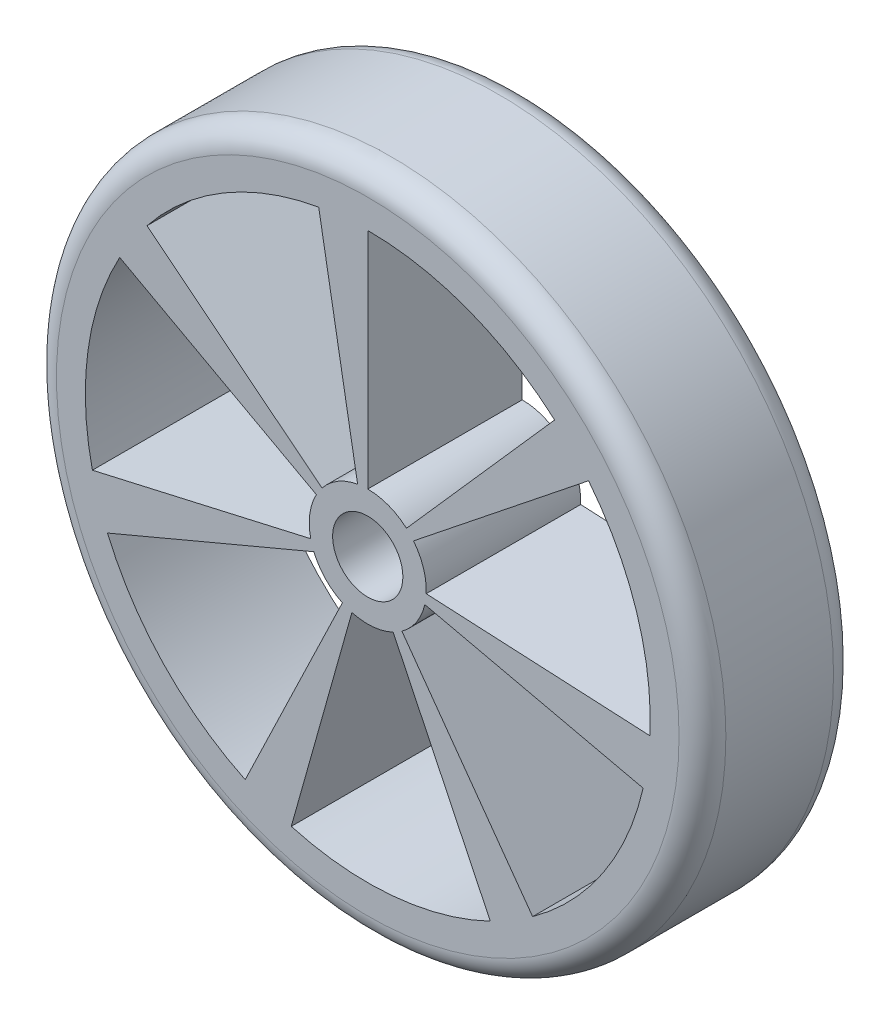
SolidWorks part; units mm, degrees
ref_plane "Ön Düzlem" through (0, 0, 0) normal (0, 0, 1) x (1, 0, 0)
ref_plane "Üst Düzlem" through (0, 0, 0) normal (0, 1, 0) x (1, 0, 0)
ref_plane "Sağ Düzlem" through (0, 0, 0) normal (1, 0, 0) x (0, 0, -1)
sketch "Sketch1" plane through (0, 0, 0) normal (0, 0, 1) x (1, 0, 0)
  circle A0 centre (0, 0) radius 14.3
  dimension "D1" = 28.6
extrude "Boss-Extrude1" add sketch "Sketch1" along normal blind 6.6
sketch "Sketch2" plane through (0, 0, 6.6) normal (0, 0, 1) x (1, 0, 0)
  line L0 (0, 2.5) -> (0, 12.0671)
  line L1 (-0.4341, 2.462) -> (-2.0954, 11.8838)
  line L2 (1.6542, 1.8745) -> (7.9846, 9.0477)
  line L3 (1.9546, 1.5587) -> (9.4344, 7.5237)
  line L4 (2.4969, -0.1246) -> (12.0521, -0.6015)
  line L5 (2.4373, -0.5563) -> (11.7645, -2.6852)
  line L6 (1.4594, -2.0298) -> (7.0441, -9.7977)
  line L7 (1.0847, -2.2524) -> (5.2357, -10.8721)
  line L8 (-0.6771, -2.4066) -> (-3.2683, -11.6161)
  line L9 (-1.0847, -2.2524) -> (-5.2357, -10.8721)
  line L10 (-2.3037, -0.9711) -> (-11.1195, -4.6873)
  line L11 (-2.4373, -0.5563) -> (-11.7645, -2.6852)
  line L12 (-2.1956, 1.1956) -> (-10.5976, 5.7711)
  line L13 (-1.9546, 1.5587) -> (-9.4344, 7.5237)
  circle A0 centre (0, 0) radius 12.0671
  circle A1 centre (0, 0) radius 2.5
  point P34 (0, 0)
  dimension "D1" = 5
  dimension "D2" = 10
  dimension "D3" = 7
fillet "Fillet1" radius 1 1 edges at (14.3, 0, 6.6)
fillet "Fillet2" radius 1 1 edges at (14.3, 0, 0)
extrude "Cut-Extrude1" cut sketch "Sketch2" against normal blind 10 contours A1 L1 A0 L13 | A1 L12 A0 L11 | A1 L10 A0 L9 | A1 L8 A0 L7 | A1 L6 A0 L5 | A1 L4 A0 L3 | A1 L2 A0 L0
sketch "Sketch3" plane through (0, 0, 6.6) normal (0, 0, 1) x (1, 0, 0)
  circle A0 centre (0, 0) radius 1.5
  dimension "D1" = 3
extrude "Cut-Extrude2" cut sketch "Sketch3" against normal blind 10
